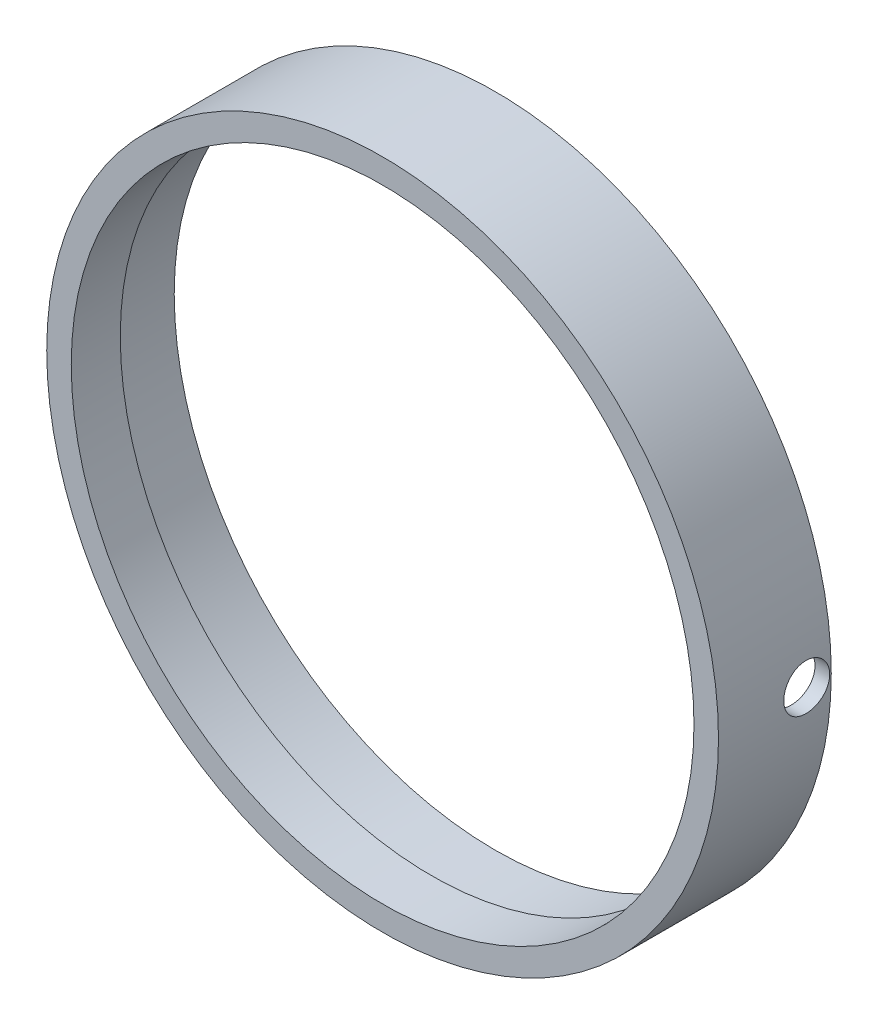
SolidWorks part; units mm, degrees
ref_plane "Front Plane" through (0, 0, 0) normal (0, 0, 1) x (1, 0, 0)
ref_plane "Top Plane" through (0, 0, 0) normal (0, 1, 0) x (1, 0, 0)
ref_plane "Right Plane" through (0, 0, 0) normal (1, 0, 0) x (0, 0, -1)
sketch "Sketch1" plane through (0, 0, 0) normal (0, 0, 1) x (1, 0, 0)
  circle A0 centre (0, 0) radius 34.798
  circle A1 centre (0, 0) radius 32.258
  dimension "D1" = 69.596
  dimension "D2" = 2.54
extrude "Boss-Extrude1" add sketch "Sketch1" along normal blind 11.684
hole_wizard "3/16 (0.1875) Diameter Hole1" positions "3DSketch1" profile "Sketch2" hole size "3/16" standard "ANSI Inch"
sketch3d "3DSketch1"
  point P4 (34.798, 0, 2.54)
sketch "Sketch2" plane through (34.798, 0, 2.54) normal (0, 1, 0) x (0, 0, -1)
  line L0 (0, 0) -> (0, 55.5328)
  line L1 (0, 55.5328) -> (2.3812, 54.102)
  line L2 (2.3812, 54.102) -> (2.3812, 0)
  line L5 (2.3812, 0) -> (0, 0)
  line L10 (0, 55.5328) -> (-2.3813, 54.102) construction
  line L11 (0, -6.35) -> (0, 107.95) construction
  dimension "Hole Dia." = 4.7625
  dimension "Hole Depth" = 54.102
  dimension "Drill Angle" = 118
sketch "Sketch3" plane through (0, 0, 0) normal (0, 0, -1) x (-1, 0, 0)
  circle A0 centre (0, 0) radius 33.274
  circle A1 centre (0, 0) radius 32.258
  dimension "D1" = 1.016
extrude "Cut-Extrude1" cut sketch "Sketch3" against normal blind 6.604
